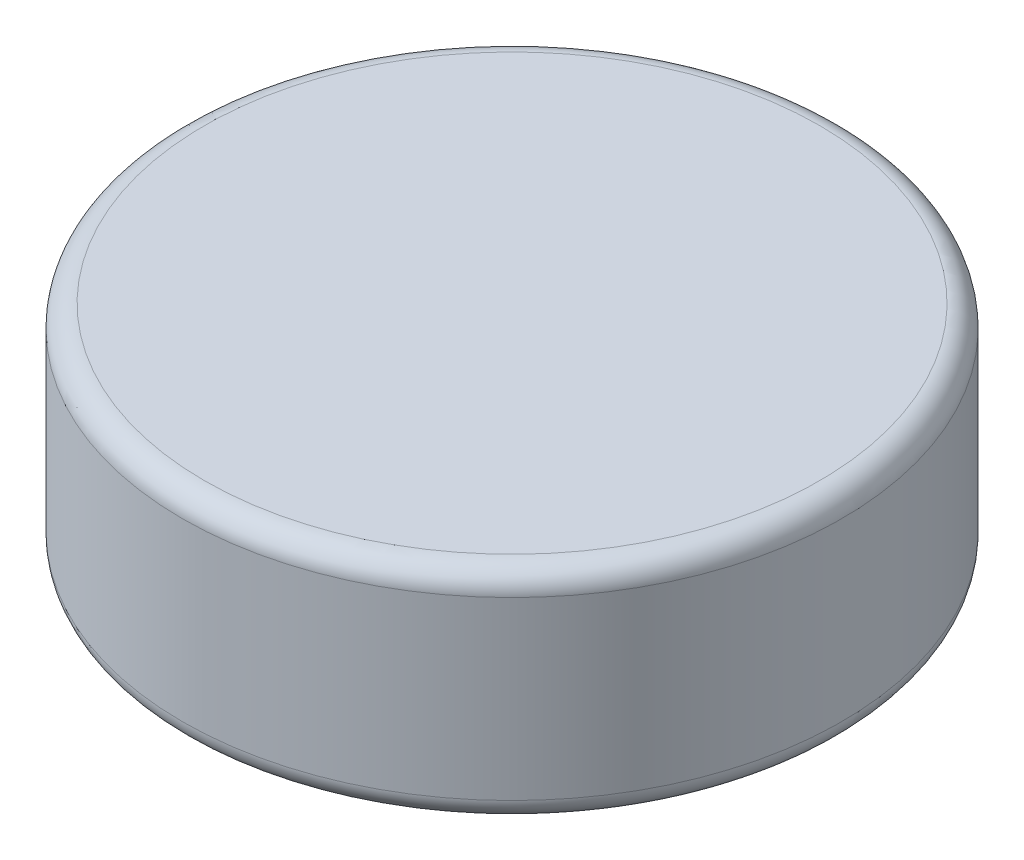
SolidWorks part; units mm, degrees
other "Camera1"
material "Titanium"
ref_plane "Front Plane" through (0, 0, 0) normal (0, 0, 1) x (1, 0, 0)
ref_plane "Top Plane" through (0, 0, 0) normal (0, 1, 0) x (1, 0, 0)
ref_plane "Right Plane" through (0, 0, 0) normal (1, 0, 0) x (0, 0, -1)
sketch "Sketch1" plane through (0, 0, 0) normal (0, 1, 0) x (1, 0, 0)
  circle A0 centre (0, 0) radius 3
  dimension "D1" = 6
extrude "Boss-Extrude1" add sketch "Sketch1" along normal blind 2 contours A0
fillet "Fillet2" radius 0.2 2 edges at (0, 2, 3) (0, 0, 3)
